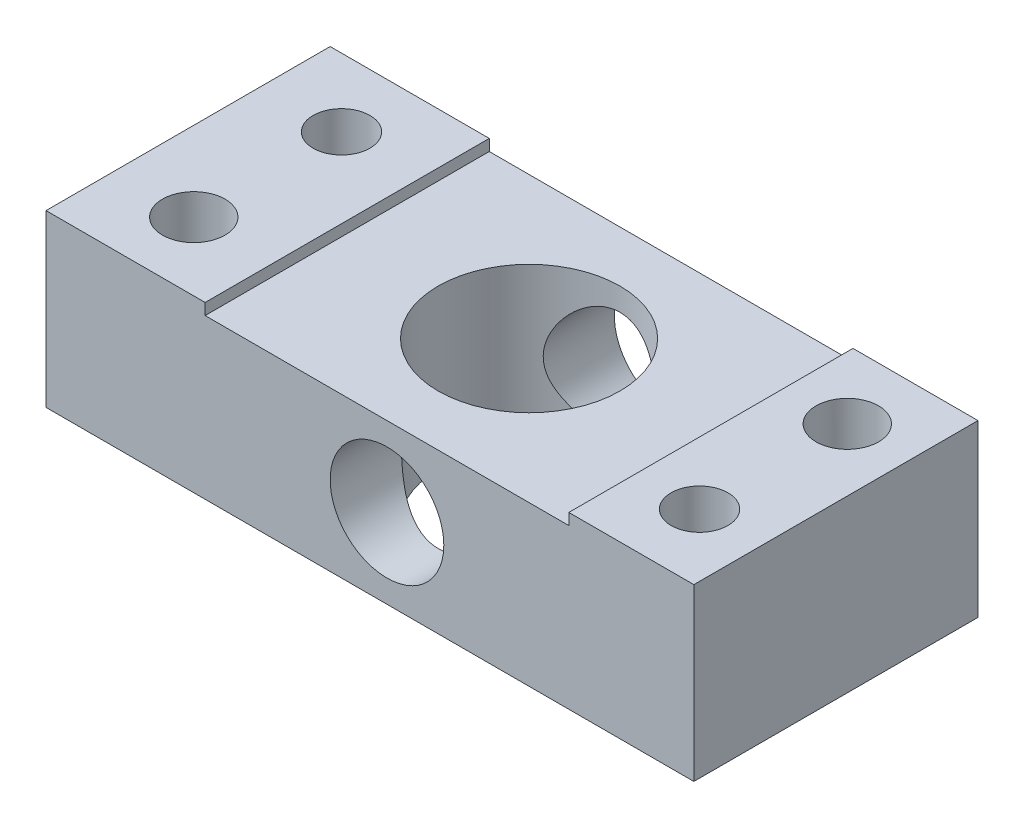
SolidWorks part; units mm, degrees
ref_plane "Front Plane" through (0, 0, 0) normal (0, 0, 1) x (1, 0, 0)
ref_plane "Top Plane" through (0, 0, 0) normal (0, 1, 0) x (1, 0, 0)
ref_plane "Right Plane" through (0, 0, 0) normal (1, 0, 0) x (0, 0, -1)
sketch "Sketch1" plane through (0, 0, 0) normal (0, 1, 0) x (1, 0, 0)
  line L1 (-28.5, 9.5) -> (28.5, 9.5)
  line L2 (-28.5, 9.5) -> (-28.5, -9.5)
  line L3 (-28.5, -9.5) -> (28.5, -9.5)
  line L4 (28.5, 9.5) -> (28.5, -9.5)
  line L5 (-28.5, 9.5) -> (28.5, -9.5) construction
  line L6 (-28.5, -9.5) -> (28.5, 9.5) construction
  point P0 (0, 0)
  dimension "D1" = 19
  dimension "D2" = 57
extrude "Boss-Extrude1" add sketch "Sketch1" along normal blind 15
sketch "Sketch2" plane through (0, 0, 9.5) normal (0, 0, 1) x (1, 0, 0)
  line L0 (-28.5, 15) -> (28.5, 15) construction
  line L1 (-14.5, 15) -> (17.5, 15)
  line L2 (-14.5, 15) -> (-14.5, 14)
  line L3 (-14.5, 14) -> (17.5, 14)
  line L4 (17.5, 15) -> (17.5, 14)
  line L5 (-28.5, 15) -> (-28.5, 0) construction
  line L6 (28.5, 15) -> (28.5, 0) construction
  dimension "D1" = 1
  dimension "D2" = 14
  dimension "D3" = 11
extrude "Cut-Extrude1" cut sketch "Sketch2" against normal blind 22
sketch "Sketch3" plane through (0, 0, 9.5) normal (0, 0, 1) x (1, 0, 0)
  line L0 (-28.5, 0) -> (28.5, 0) construction
  circle A0 centre (0, 7) radius 5
  dimension "D1" = 7
extrude "Cut-Extrude2" cut sketch "Sketch3" against normal blind 22
sketch "Sketch5" plane through (0, 0, 9.5) normal (0, 0, 1) x (1, 0, 0)
  line L0 (-28.5, 15) -> (-14.5, 15)
  line L1 (-14.5, 15) -> (-14.5, 14)
  line L2 (-14.5, 14) -> (17.5, 14)
  line L3 (17.5, 14) -> (17.5, 15)
  line L4 (17.5, 15) -> (28.5, 15)
  line L5 (28.5, 15) -> (28.5, 0)
  line L6 (28.5, 0) -> (-28.5, 0)
  line L7 (-28.5, 0) -> (-28.5, 15)
extrude "Boss-Extrude2" add sketch "Sketch5" along normal blind 6
sketch "Sketch6" plane through (0, 0, 0) normal (0, -1, 0) x (1, 0, 0)
  line L1 (28.5, 15.5) -> (28.5, -9.5) construction
  line L2 (-28.5, -9.5) -> (-28.5, 15.5) construction
  line L3 (28.5, -9.5) -> (-28.5, -9.5) construction
  line L4 (-28.5, 15.5) -> (28.5, 15.5) construction
  circle A0 centre (-21.5, 9.5) radius 2.75
  circle A1 centre (23, -3.5) radius 2.75
  circle A2 centre (-21.5, -3.5) radius 2.5
  circle A3 centre (23, 9.5) radius 2.5
  dimension "D1" = 5.5
  dimension "D5" = 6
  dimension "D2" = 7
  dimension "D3" = 6
  dimension "D4" = 6
  dimension "D6" = 6
  dimension "D7" = 7
extrude "Cut-Extrude5" cut sketch "Sketch6" against normal blind 58.7
sketch "Sketch8" plane through (0, 0, 0) normal (0, -1, 0) x (1, 0, 0)
  circle A0 centre (-21.5, 9.5) radius 5
  circle A1 centre (23, -3.5) radius 5
extrude "Cut-Extrude6" cut sketch "Sketch8" against normal blind 5.7
sketch "Sketch9" plane through (0, 0, 0) normal (0, -1, 0) x (1, 0, 0)
  line L0 (28.5, -9.5) -> (-28.5, -9.5) construction
  circle A0 centre (0, 3) radius 8
  dimension "D1" = 12.5
extrude "Cut-Extrude7" cut sketch "Sketch9" against normal blind 15.7
sketch "Sketch10" plane through (0, 0, -9.5) normal (0, 0, -1) x (-1, 0, 0)
  circle A0 centre (0, 7) radius 5
extrude "Cut-Extrude8" cut sketch "Sketch10" against normal blind 56.7
sketch "Sketch11" plane through (0, 0, 0) normal (0, -1, 0) x (1, 0, 0)
  circle A0 centre (0, 3) radius 8
extrude "Boss-Extrude3" add sketch "Sketch11" against normal up to surface (14 mm away) up to face at (0, 14, -5)
sketch "Sketch12" plane through (0, 0, 15.5) normal (0, 0, 1) x (1, 0, 0)
  circle A0 centre (0, 7) radius 5
extrude "Boss-Extrude4" add sketch "Sketch12" against normal up to surface (25 mm away) up to face at (5, 7, -9.5)
sketch "Sketch13" plane through (0, 0, 0) normal (0, -1, 0) x (1, 0, 0)
  line L0 (28.5, -9.5) -> (-28.5, -9.5) construction
  line L1 (-28.5, -9.5) -> (-28.5, 15.5) construction
  circle A0 centre (1.5, 3) radius 8
  dimension "D1" = 12.5
  dimension "D2" = 30
extrude "Cut-Extrude9" cut sketch "Sketch13" against normal blind 171
sketch "Sketch14" plane through (0, 0, 15.5) normal (0, 0, 1) x (1, 0, 0)
  line L0 (-28.5, 0) -> (28.5, 0) construction
  line L1 (-28.5, 15) -> (-28.5, 0) construction
  circle A0 centre (1.5, 7) radius 5
  dimension "D1" = 7
  dimension "D2" = 30
extrude "Cut-Extrude10" cut sketch "Sketch14" against normal blind 171
